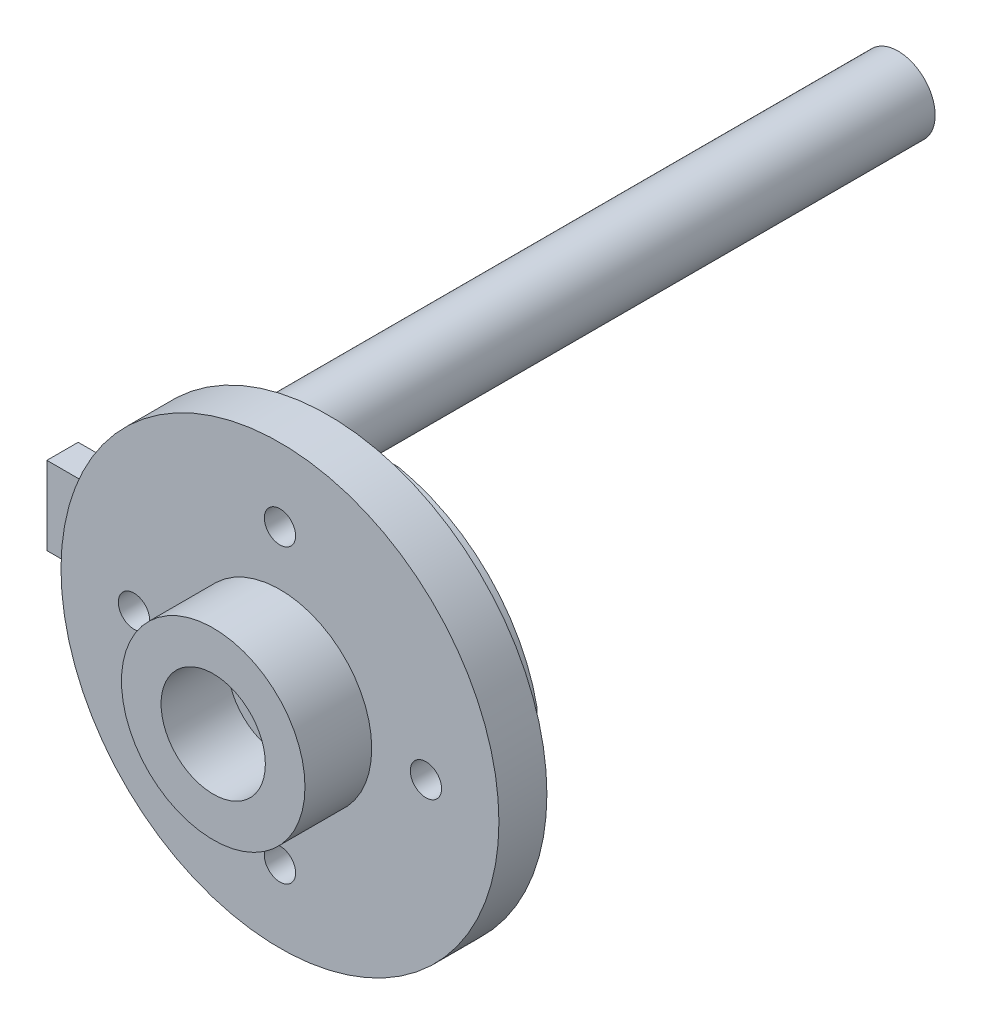
SolidWorks part; units mm, degrees
ref_plane "Front" through (0, 0, 0) normal (0, 0, 1) x (1, 0, 0)
ref_plane "Top" through (0, 0, 0) normal (0, 1, 0) x (1, 0, 0)
ref_plane "Right" through (0, 0, 0) normal (1, 0, 0) x (0, 0, -1)
sketch "Sketch1" plane through (0, 0, 0) normal (0, 0, 1) x (1, 0, 0)
  circle A0 centre (0, 0) radius 10.5
  dimension "D1" = 21
extrude "Boss-Extrude1" add sketch "Sketch1" along normal blind 2.3
sketch "Sketch2" plane through (0, 0, 2.3) normal (0, 0, 1) x (1, 0, 0)
  line L0 (0, 0) -> (0, 10.5) construction
  circle A0 centre (0, 0) radius 10.5 construction
  circle A1 centre (0, 7) radius 0.75
  dimension "D1" = 1.5
  dimension "D2" = 7
extrude "Cut-Extrude1" cut sketch "Sketch2" against normal through all
sketch "Sketch3" plane through (0, 0, 2.3) normal (0, 0, 1) x (1, 0, 0)
  circle A0 centre (0, 0) radius 1.5
  dimension "D1" = 3
extrude "Cut-Extrude2" cut sketch "Sketch3" against normal blind 2.3
pattern_circular "CirPattern1" count 4 over 360 about axis through (0, 0, 0) along (0, 0, 1) of "Cut-Extrude1"
sketch "Sketch4" plane through (0, 0, 2.3) normal (0, 0, 1) x (1, 0, 0)
  circle A0 centre (0, 0) radius 4.4
  circle A1 centre (0, 0) radius 2.5
  dimension "D1" = 8.8
  dimension "D2" = 5
extrude "Boss-Extrude2" add sketch "Sketch4" along normal blind 3.2
sketch "Sketch5" plane through (0, 0, 0) normal (0, 0, -1) x (-1, 0, 0)
  line L1 (-8.5242, 1.875) -> (13.4758, 1.875)
  line L2 (-8.5242, 1.875) -> (-8.5242, -1.875)
  line L3 (-8.5242, -1.875) -> (13.4758, -1.875)
  line L4 (13.4758, 1.875) -> (13.4758, -1.875)
  circle A0 centre (10.16, 0) radius 1.778
  circle A1 centre (-7, 0) radius 0.75
  circle A2 centre (7, 0) radius 0.75
  point P4 (-8.5242, 0)
  circle M5 centre (7, 0) radius 0.75
  circle M7 centre (-7, 0) radius 0.75
  circle M8 centre (0, 0) radius 1.5
  circle M10 centre (0, 0) radius 10.5
  dimension "D2" = 3.556
  dimension "D1" = 3.75
  dimension "D3" = 10.16
  dimension "D4" = 22
extrude "Boss-Extrude3" add sketch "Sketch5" along normal blind 1.5 contours A0 M10 | A0 M10 | A0 L1 L2 L3 M10 M5 M7 M8 | A0 L3 L4 L1 M10
sketch "Sketch6" plane through (0, 0, -1.5) normal (0, 0, -1) x (-1, 0, 0)
  circle A0 centre (10.16, 0) radius 1.778
  dimension "D2" = 3.556
  dimension "D1" = 10.16
extrude "Boss-Extrude4" add sketch "Sketch6" along normal blind 36
sketch "Sketch7" plane through (0, 0, 0) normal (0, 0, -1) x (-1, 0, 0)
  line L0 (-8.5242, 1.875) -> (10.3312, 1.875) construction
  line L1 (-1.875, 1.875) -> (1.875, 1.875)
  line L2 (-1.875, 1.875) -> (-1.875, 8.5241)
  line L3 (-1.875, 8.5241) -> (1.875, 8.5241)
  line L4 (1.875, 1.875) -> (1.875, 8.5241)
  line L5 (-8.5242, -1.875) -> (13.4758, -1.875) construction
  line L6 (-1.875, -1.875) -> (1.875, -1.875)
  line L7 (-1.875, -1.875) -> (-1.875, -8.5241)
  line L8 (-1.875, -8.5241) -> (1.875, -8.5241)
  line L9 (1.875, -1.875) -> (1.875, -8.5241)
  line L10 (-8.5242, 1.875) -> (13.4758, 1.875) construction
  line L11 (-8.5242, -1.875) -> (10.3312, -1.875) construction
  arc A0 (-1.875, 8.5241) -> (-8.5242, 1.875) centre (-0.1719, 0.1719) ccw
  arc A1 (1.875, 8.5241) -> (8.5241, 1.875) centre (0.1719, 0.1719) cw
  arc A2 (-1.875, -8.5241) -> (-8.5242, -1.875) centre (-0.1719, -0.1719) cw
  arc A3 (8.5241, -1.875) -> (1.875, -8.5241) centre (0.1719, -0.1719) cw
  circle A4 centre (0, 7) radius 0.75
  circle A5 centre (0, -7) radius 0.75
  point P15 (0, 8.5241)
  point P17 (0, -8.5241)
  circle M1 centre (0, 7) radius 0.75
  circle M2 centre (0, -7) radius 0.75
  line M3 (10.3312, -1.875) -> (-8.5242, -1.875)
  line M5 (-8.5242, 1.875) -> (10.3312, 1.875)
  dimension "D5" = 8.5241
  dimension "D7" = 8.5241
  dimension "D8" = 8.5241
  dimension "D10" = 8.5241
  dimension "D1" = 3.75
  dimension "D2" = 3.75
  dimension "D3" = 8.5241
  dimension "D4" = 8.5241
  dimension "D6" = 8.5241
  dimension "D9" = 8.5241
extrude "Boss-Extrude5" add sketch "Sketch7" along normal blind 1.5 contours L2 A0 M5 | A1 L4 M5 | A2 L7 M3 | A3 L9 M3 | L9 L7 L8 M3 M2 | L4 L3 L2 M5 M1
